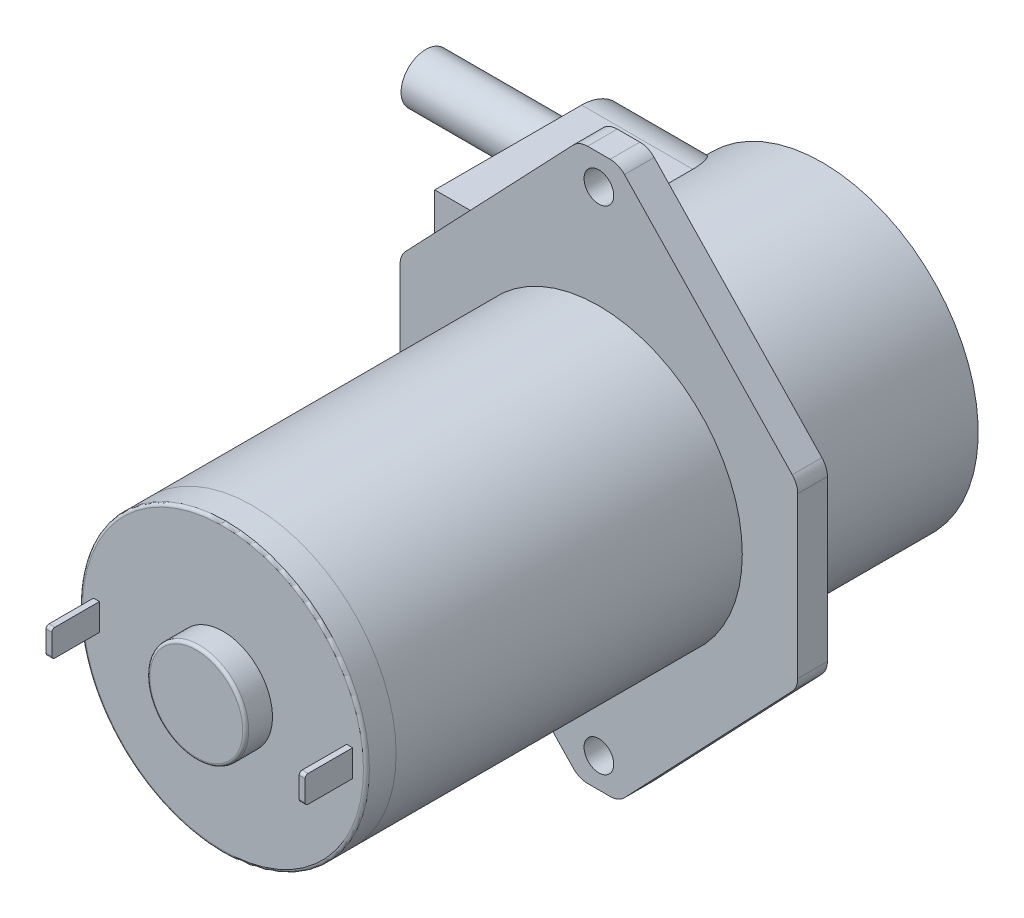
SolidWorks part; units mm, degrees
ref_plane "Front Plane" through (0, 0, 0) normal (0, 0, 1) x (1, 0, 0)
ref_plane "Top Plane" through (0, 0, 0) normal (0, 1, 0) x (1, 0, 0)
ref_plane "Right Plane" through (0, 0, 0) normal (1, 0, 0) x (0, 0, -1)
sketch "Sketch1" plane through (0, 0, 0) normal (0, 0, 1) x (1, 0, 0)
  circle A0 centre (0, 0) radius 14.5
  dimension "D1" = 29
extrude "Boss-Extrude1" add sketch "Sketch1" along normal blind 35
ref_plane "Plane1" through (0, 0, 35) normal (0, 0, 1) x (1, 0, 0)
sketch "Sketch3" plane through (0, 0, 35) normal (0, 0, 1) x (1, 0, 0)
  circle A0 centre (0, 0) radius 14.5 construction
  circle A1 centre (0, 0) radius 14.5
extrude "Boss-Extrude2" add sketch "Sketch3" along normal blind 3 separate body
ref_plane "Plane2" through (0, 0, 38) normal (0, 0, -1) x (-1, 0, 0)
sketch "Sketch5" plane through (0, 0, 38) normal (0, 0, -1) x (-1, 0, 0)
  circle A0 centre (0, 0) radius 5
  dimension "D1" = 10
extrude "Boss-Extrude3" add sketch "Sketch5" against normal blind 2.7
sketch "Sketch6" plane through (0, 0, 38) normal (0, 0, -1) x (-1, 0, 0)
  line L0 (14.5, 0) -> (-14.5, 0) construction
  line L1 (0, 14.5) -> (0, -14.5) construction
  line L2 (-12.5, -1.35) -> (-13.1, -1.35)
  line L3 (-12.5, -1.35) -> (-12.5, 1.35)
  line L4 (-12.5, 1.35) -> (-13.1, 1.35)
  line L5 (-13.1, -1.35) -> (-13.1, 1.35)
  line L6 (-12.5, -1.35) -> (-13.1, 1.35) construction
  line L7 (-12.5, 1.35) -> (-13.1, -1.35) construction
  line L8 (12.5, -1.35) -> (12.5, 1.35)
  line L9 (12.5, -1.35) -> (13.1, -1.35)
  line L10 (13.1, -1.35) -> (13.1, 1.35)
  line L11 (12.5, 1.35) -> (13.1, 1.35)
  circle A0 centre (0, 0) radius 14.5 construction
  point P5 (-12.8, 0)
  dimension "D1" = 2.7
  dimension "D2" = 0.6
  dimension "D3" = 1.4
extrude "Boss-Extrude4" add sketch "Sketch6" against normal blind 4.8
fillet "Fillet1" radius 0.3 6 edges at (12.8, -1.35, 42.8) (12.8, 1.35, 42.8) (-12.8, -1.35, 42.8) (-12.8, 1.35, 42.8) (14.5, 0, 38) (-5, 0, 40.7)
sketch "Sketch7" plane through (0, 0, 0) normal (0, 0, 1) x (1, 0, 0)
  line L0 (19.5481, 9.4793) -> (2.5911, 27.2795)
  line L1 (20.1, -8.9) -> (-20.1, -8.9) construction
  line L2 (20.1, -8.9) -> (20.1, 8.9) construction
  line L3 (20.1, 8.9) -> (-20.1, 8.9) construction
  line L4 (-20.1, -8.9) -> (-20.1, 8.9) construction
  line L5 (20.1, -8.9) -> (-20.1, 8.9) construction
  line L6 (20.1, 8.9) -> (-20.1, -8.9) construction
  line L7 (1.143, 27.9) -> (-1.143, 27.9)
  line L8 (-2.5911, 27.2795) -> (-19.5481, 9.4793)
  line L9 (0, 0) -> (0, 27.9) construction
  line L10 (0, 27.9) -> (0, 14.5) construction
  line L11 (0, 26.4) -> (0, 27.9) construction
  line L12 (-20.1, 0) -> (20.1, 0) construction
  line L13 (20.1, 8.0998) -> (20.1, -8.0998)
  line L14 (-20.1, 8.0998) -> (-20.1, -8.0998)
  line L15 (-2.5911, -27.2795) -> (-19.5481, -9.4793)
  line L16 (1.143, -27.9) -> (-1.143, -27.9)
  line L17 (19.5481, -9.4793) -> (2.5911, -27.2795)
  circle A0 centre (0, 24.9) radius 1.5
  circle A1 centre (0, 0) radius 14.5 construction
  arc A2 (19.5481, 9.4793) -> (20.1, 8.0998) centre (18.1, 8.0998) cw
  arc A3 (-20.1, 8.0998) -> (-19.5481, 9.4793) centre (-18.1, 8.0998) cw
  arc A4 (-1.143, 27.9) -> (-2.5911, 27.2795) centre (-1.143, 25.9) ccw
  arc A5 (2.5911, 27.2795) -> (1.143, 27.9) centre (1.143, 25.9) ccw
  arc A6 (-20.1, -8.0998) -> (-19.5481, -9.4793) centre (-18.1, -8.0998) ccw
  arc A7 (-1.143, -27.9) -> (-2.5911, -27.2795) centre (-1.143, -25.9) cw
  circle A8 centre (0, -24.9) radius 1.5
  arc A9 (2.5911, -27.2795) -> (1.143, -27.9) centre (1.143, -25.9) cw
  arc A10 (19.5481, -9.4793) -> (20.1, -8.0998) centre (18.1, -8.0998) ccw
  point P0 (0, 0)
  point P13 (0, 27.9)
  point P19 (5.2063, 27.9)
  point P28 (-2, 27.9)
  point P31 (2, 27.9)
  dimension "D1" = 3
  dimension "D7" = 2
  dimension "D2" = 40.2
  dimension "D3" = 17.8
  dimension "D4" = 13.4
  dimension "D5" = 1.5
  dimension "D6" = 4
extrude "Boss-Extrude5" add sketch "Sketch7" against normal blind 3
ref_plane "Plane3" through (0, 0, -3) normal (0, 0, -1) x (-1, 0, 0)
sketch "Sketch8" plane through (0, 0, -3) normal (0, 0, -1) x (-1, 0, 0)
  line L0 (15.75, 0) -> (-15.75, 0) construction
  line L1 (19.6, 3.85) -> (15.2722, 3.85)
  line L2 (8.357, 13.35) -> (19.6, 13.35)
  line L3 (8.357, 13.35) -> (8.357, 3.85) construction
  line L4 (8.357, 3.85) -> (19.6, 3.85) construction
  line L5 (19.6, 13.35) -> (19.6, 3.85)
  line L6 (19.6, -3.85) -> (15.2722, -3.85)
  line L7 (19.6, -13.35) -> (19.6, -3.85)
  line L8 (8.357, -13.35) -> (19.6, -13.35)
  circle A0 centre (0, 0) radius 15.75
  dimension "D1" = 31.5
  dimension "D2" = 9.5
  dimension "D3" = 3.85
  dimension "D4" = 19.6
extrude "Boss-Extrude6" add sketch "Sketch8" along normal blind 19.6 contours A0 | A0 L1 L5 L2 | A0 L8 L7 L6
ref_plane "Plane4" through (-19.6, 0, 0) normal (-1, 0, 0) x (0, 0, 1)
sketch "Sketch9" plane through (-19.6, 0, 0) normal (-1, 0, 0) x (0, 0, 1)
  line L0 (-22.6, -8.6) -> (-3, -8.6) construction
  line L1 (-22.6, -13.35) -> (-22.6, -3.85) construction
  line L2 (-3, 19.7784) -> (-3, -19.7784) construction
  line L3 (-22.6, -3.85) -> (-3, -3.85) construction
  line L4 (-17.85, -3.85) -> (-22.6, -3.85)
  line L5 (-22.6, -3.85) -> (-22.6, -13.35)
  line L6 (-22.6, -13.35) -> (-17.85, -13.35)
  line L7 (0, 0) -> (-27.2154, 0) construction
  line L8 (-22.6, 13.35) -> (-17.85, 13.35)
  line L9 (-22.6, 3.85) -> (-22.6, 13.35)
  line L10 (-17.85, 3.85) -> (-22.6, 3.85)
  circle A0 centre (-17.85, -8.6) radius 4.75
  circle A1 centre (-17.85, 8.6) radius 4.75
extrude "Cut-Extrude1" cut sketch "Sketch9" against normal up to surface (11.243 mm away) contours L9 A1 L8 | L10 A1 L9 | A0 L4 L5 | A0 L5 L6
sketch "Sketch10" plane through (-19.6, 0, 0) normal (-1, 0, 0) x (0, 0, 1)
  line L0 (-22.6, -8.6) -> (-3, -8.6) construction
  line L1 (-3, 19.7784) -> (-3, -19.7784) construction
  line L2 (0, 0) -> (-25.8449, 0) construction
  line L3 (-19.6, -8.6) -> (-22.6, -8.6) construction
  arc A0 (-17.85, -3.85) -> (-17.85, -13.35) centre (-17.85, -8.6) ccw construction
  circle A1 centre (-17.1, -8.6) radius 2.5
  circle A2 centre (-17.1, -8.6) radius 1.5
  circle A3 centre (-17.1, 8.6) radius 1.5
  circle A4 centre (-17.1, 8.6) radius 2.5
  dimension "D1" = 5
  dimension "D2" = 3
  dimension "D3" = 3
extrude "Boss-Extrude7" add sketch "Sketch10" along normal blind 15 contours A4 A3 | A1 A2
